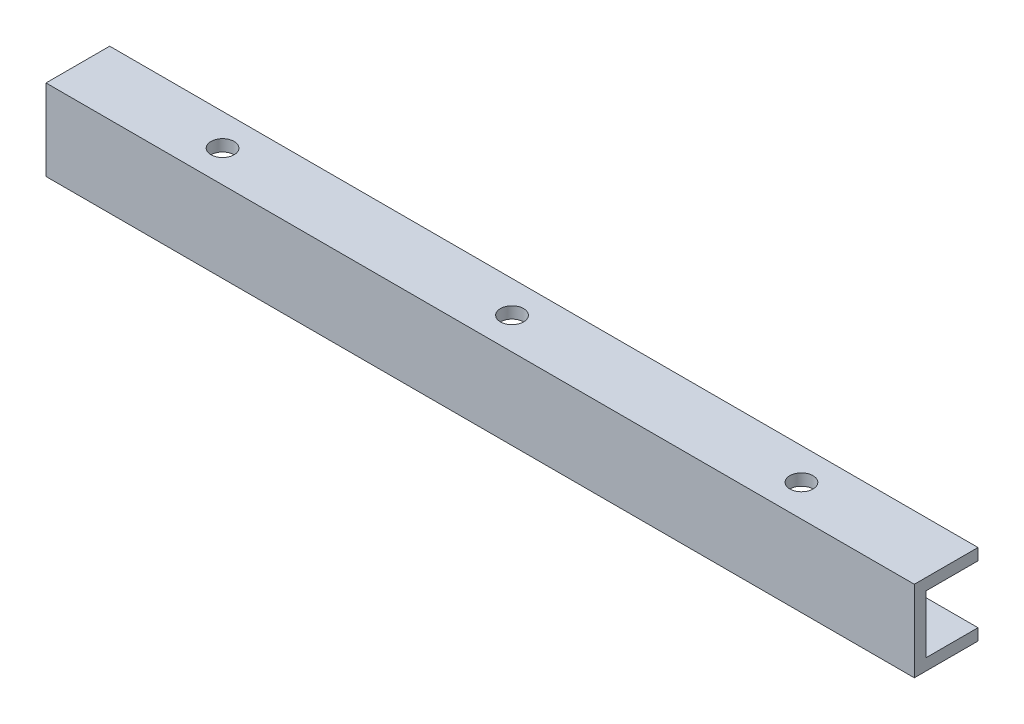
SolidWorks part; units mm, degrees
ref_plane "Front Plane" through (0, 0, 0) normal (0, 0, 1) x (1, 0, 0)
ref_plane "Top Plane" through (0, 0, 0) normal (0, 1, 0) x (1, 0, 0)
ref_plane "Right Plane" through (0, 0, 0) normal (1, 0, 0) x (0, 0, -1)
sketch "Sketch1" plane through (0, 0, 0) normal (1, 0, 0) x (0, 0, -1)
  line L0 (0, 0) -> (-10, 0)
  line L1 (-10, 0) -> (-10, -12)
  line L2 (-10, -12) -> (0, -12)
  point P5 (0, 0)
  dimension "D1" = 10
  dimension "D2" = 12
surface "Surface-Extrude1" sketch "Sketch1" parameters "D1"=150
thicken "Thicken1" surfaces to thicken 101 thickness 1 thickness side both sides parameters "D1"=1
sketch "Sketch2" plane through (0, 1, 0) normal (0, 1, 0) x (1, 0, 0)
  line L0 (-150, -5.5) -> (0, -5.5) construction
  line L1 (-150, 0) -> (-150, -11) construction
  line L2 (0, 0) -> (0, -11) construction
  line L3 (-25, -16.1476) -> (-25, 9.939) construction
  line L4 (-75, -16.1476) -> (-75, 9.939) construction
  line L5 (-125, -18.5433) -> (-125, 7.5433) construction
  line L6 (-125, -18.5433) -> (-125, 12.0685) construction
  point P12 (-75, -5.5)
  point P16 (-25, -5.5)
  point P17 (-125, -5.5)
  dimension "D1" = 25
  dimension "D2" = 50
  dimension "D3" = 25
  dimension "D4" = 50
hole_wizard "Ø4.0mm Dowel Hole1" positions "Sketch3" profile "Sketch4" hole size "Ø4.0" standard "BSI" end condition through all
sketch "Sketch3" plane through (0, 1, 0) normal (0, 1, 0) x (1, 0, 0)
  point P0 (-125, -5.5)
  point P3 (-75, -5.5)
  point P6 (-25, -5.5)
sketch "Sketch4" plane through (-125, 1, 5.5) normal (1, 0, 0) x (0, 0, 1)
  line L0 (0, 0) -> (0, 14)
  line L1 (0, 14) -> (2, 14)
  line L2 (2, 14) -> (2, 0)
  line L5 (2, 0) -> (0, 0)
  line L11 (0, -6.35) -> (0, 107.95) construction
  dimension "Thru Hole Dia." = 4
  dimension "Thru Hole Depth" = 14
